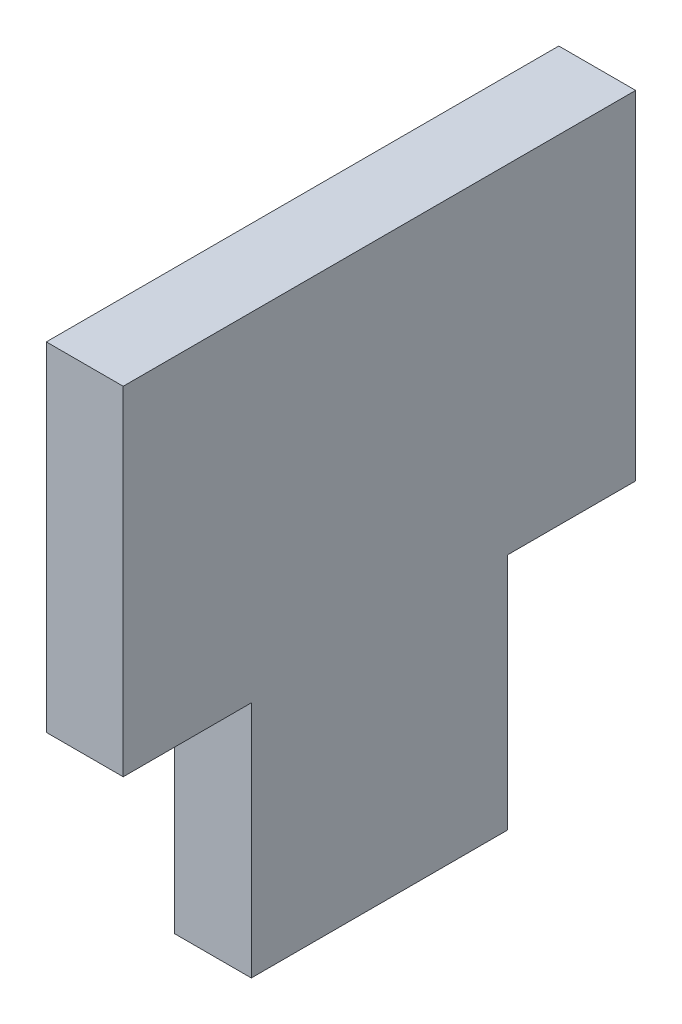
SolidWorks part; units mm, degrees
ref_plane "Front Plane" through (0, 0, 0) normal (0, 0, 1) x (1, 0, 0)
ref_plane "Top Plane" through (0, 0, 0) normal (0, 1, 0) x (1, 0, 0)
ref_plane "Right Plane" through (0, 0, 0) normal (1, 0, 0) x (0, 0, -1)
sketch "Sketch1" plane through (0, 0, 0) normal (1, 0, 0) x (0, 0, -1)
  line L0 (-5, -6.6) -> (-5, -15.9)
  line L1 (-10, -6.6) -> (-5, -6.6)
  line L2 (-10, -6.6) -> (-10, 6.6)
  line L3 (-10, 6.6) -> (10, 6.6)
  line L4 (10, -6.6) -> (10, 6.6)
  line L5 (-10, -6.6) -> (10, 6.6) construction
  line L6 (-10, 6.6) -> (10, -6.6) construction
  line L7 (-5, -15.9) -> (5, -15.9)
  line L8 (5, -15.9) -> (5, -6.6)
  line L9 (5, -6.6) -> (10, -6.6)
  point P0 (0, 0)
  dimension "D1" = 20
  dimension "D2" = 13.2
  dimension "D3" = 10
  dimension "D4" = 9.3
  dimension "D5" = 5
extrude "Boss-Extrude1" add sketch "Sketch1" along normal blind 3
